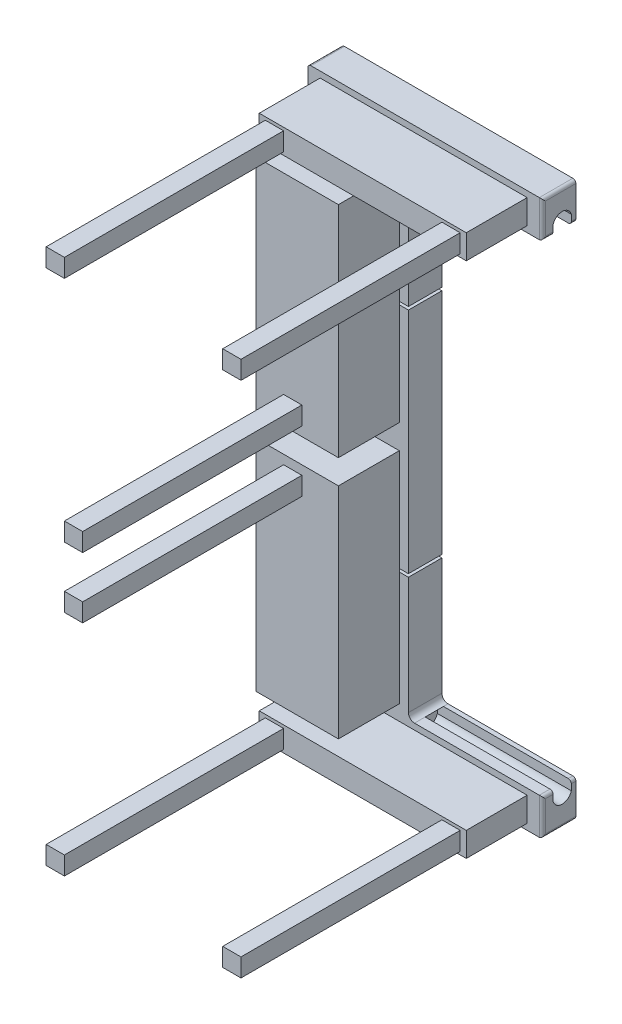
SolidWorks part; units mm, degrees
ref_plane "Front Plane" through (0, 0, 0) normal (0, 0, 1) x (1, 0, 0)
ref_plane "Top Plane" through (0, 0, 0) normal (0, 1, 0) x (1, 0, 0)
ref_plane "Right Plane" through (0, 0, 0) normal (1, 0, 0) x (0, 0, -1)
sketch "Sketch1" plane through (0, 0, 0) normal (0, 0, 1) x (1, 0, 0)
  line L0 (977.9, -152.4) -> (419.1, -152.4)
  line L1 (0, 0) -> (977.9, 0)
  line L2 (0, 0) -> (0, -2311.4)
  line L3 (0, -2311.4) -> (977.9, -2311.4)
  line L4 (977.9, 0) -> (977.9, -152.4)
  line L5 (419.1, -152.4) -> (419.1, -2159)
  line L6 (419.1, -2159) -> (977.9, -2159)
  line L7 (977.9, -2159) -> (977.9, -2311.4)
  dimension "D1" = 2311.4
  dimension "D2" = 977.9
  dimension "D3" = 152.4
  dimension "D4" = 152.4
  dimension "D5" = 419.1
extrude "Boss-Extrude1" add sketch "Sketch1" along normal blind 241.3
fillet "Fillet1" radius 25.4 2 edges at (419.1, -2159, 120.65) (419.1, -152.4, 120.65)
fillet "Fillet2" radius 12.7 10 edges at (977.9, -76.2, 0) (977.9, -76.2, 241.3) (977.9, -2235.2, 0) (977.9, -2235.2, 241.3) (977.9, -152.4, 120.65) (977.9, 0, 120.65) (0, 0, 120.65) (0, -2311.4, 120.65) (977.9, -2311.4, 120.65) (977.9, -2159, 120.65)
sketch "Sketch2" plane through (977.9, 0, 0) normal (1, 0, 0) x (0, 0, -1)
  line L0 (-196.85, -152.4) -> (-196.85, -114.3)
  line L1 (-241.3, -152.4) -> (0, -152.4) construction
  line L2 (-196.85, -152.4) -> (-120.61, -152.4)
  line L3 (-120.61, -152.4) -> (-120.61, -114.3)
  line L4 (-241.3, -2133.6) -> (-241.3, -177.8) construction
  arc A0 (-196.85, -114.3) -> (-120.61, -114.3) centre (-158.73, -124.7257) cw
  dimension "D2" = 39.52
  dimension "D1" = 38.1
  dimension "D3" = 76.24
  dimension "D4" = 82.57
extrude "Cut-Extrude1" cut sketch "Sketch2" against normal up to surface (558.8 mm away) up to face at (419.1, -1155.7, 120.65)
ref_plane "Plane1" through (0, -1155.7, 0) normal (0, 1, 0) x (1, 0, 0)
mirror "Mirror1" about plane through (0, -1155.7, 0) normal (0, 1, 0) of "Cut-Extrude1"
sketch "Sketch3" plane through (0, 0, 0) normal (0, 0, -1) x (-1, 0, 0)
  line L1 (-1029.2158, 57.614) -> (84.8781, 57.614)
  line L2 (-1029.2158, 57.614) -> (-1029.2158, -2397.8268)
  line L3 (-1029.2158, -2397.8268) -> (84.8781, -2397.8268)
  line L4 (84.8781, 57.614) -> (84.8781, -2397.8268)
extrude "Cut-Extrude5" cut sketch "Sketch3" against normal blind 101.6
sketch "Sketch4" plane through (419.1, 0, 0) normal (1, 0, 0) x (0, 0, -1)
  line L0 (-241.3, -2133.6) -> (-241.3, -177.8) construction
  line L1 (-101.6, -666.75) -> (-241.3, -666.75)
  line L2 (-101.6, -666.75) -> (-101.6, -679.45)
  line L3 (-101.6, -679.45) -> (-241.3, -679.45)
  line L4 (-241.3, -666.75) -> (-241.3, -679.45)
  line L5 (-101.6, -666.75) -> (-241.3, -679.45) construction
  line L6 (-101.6, -679.45) -> (-241.3, -666.75) construction
  line L7 (-101.6, -177.8) -> (-101.6, -2133.6) construction
  line L8 (-241.3, 0) -> (-101.6, 0) construction
  point P0 (-171.45, -673.1)
  dimension "D1" = 673.1
  dimension "D2" = 12.7
extrude "Cut-Extrude6" cut sketch "Sketch4" against normal blind 401.32
mirror "Mirror2" about plane through (0, -1155.7, 0) normal (0, 1, 0) of "Cut-Extrude6"
sketch "Sketch9" plane through (0, 0, 241.3) normal (0, 0, 1) x (1, 0, 0)
  line L0 (965.2, 0) -> (12.7, 0) construction
  line L1 (50.8, -25.4) -> (914.4, -25.4)
  line L2 (50.8, -25.4) -> (50.8, -127)
  line L3 (50.8, -127) -> (914.4, -127)
  line L4 (914.4, -25.4) -> (914.4, -127)
  line L5 (0, -12.7) -> (0, -2298.7) construction
  line L6 (965.2, -152.4) -> (965.2, 0) construction
  line L7 (444.5, -152.4) -> (965.2, -152.4) construction
  line L8 (76.835, -1155.7) -> (-76.835, -1155.7) construction
  line L9 (38.1, -190.5) -> (381, -190.5)
  line L10 (38.1, -190.5) -> (38.1, -1104.9)
  line L11 (38.1, -1104.9) -> (381, -1104.9)
  line L12 (381, -190.5) -> (381, -1104.9)
  line L13 (419.1, -666.75) -> (419.1, -177.8) construction
  dimension "D1" = 25.4
  dimension "D2" = 50.8
  dimension "D3" = 50.8
  dimension "D4" = 25.4
  dimension "D5" = 38.1
  dimension "D6" = 914.4
  dimension "D7" = 50.8
  dimension "D8" = 38.1
extrude "Boss-Extrude5" add sketch "Sketch9" along normal blind 254
sketch "Sketch10" plane through (0, 0, 495.3) normal (0, 0, 1) x (1, 0, 0)
  line L0 (965.2, 0) -> (12.7, 0) construction
  line L1 (76.2, -38.1) -> (152.4, -38.1)
  line L2 (76.2, -38.1) -> (76.2, -114.3)
  line L3 (76.2, -114.3) -> (152.4, -114.3)
  line L4 (152.4, -38.1) -> (152.4, -114.3)
  line L5 (812.8, -38.1) -> (889, -38.1)
  line L6 (812.8, -38.1) -> (812.8, -114.3)
  line L7 (812.8, -114.3) -> (889, -114.3)
  line L8 (889, -38.1) -> (889, -114.3)
  line L9 (152.4, -990.6) -> (228.6, -990.6)
  line L10 (152.4, -990.6) -> (152.4, -1066.8)
  line L11 (152.4, -1066.8) -> (228.6, -1066.8)
  line L12 (228.6, -990.6) -> (228.6, -1066.8)
  line L13 (0, -12.7) -> (0, -2298.7) construction
  line L14 (965.2, -152.4) -> (965.2, 0) construction
  line L15 (216.535, -1155.7) -> (-216.535, -1155.7) construction
  dimension "D1" = 38.1
  dimension "D2" = 76.2
  dimension "D3" = 76.2
  dimension "D4" = 38.1
  dimension "D5" = 76.2
  dimension "D6" = 152.4
  dimension "D7" = 88.9
extrude "Boss-Extrude6" add sketch "Sketch10" along normal blind 914.4
mirror "Mirror4" about plane through (0, -1155.7, 0) normal (0, 1, 0) of "Boss-Extrude6", "Boss-Extrude5"
